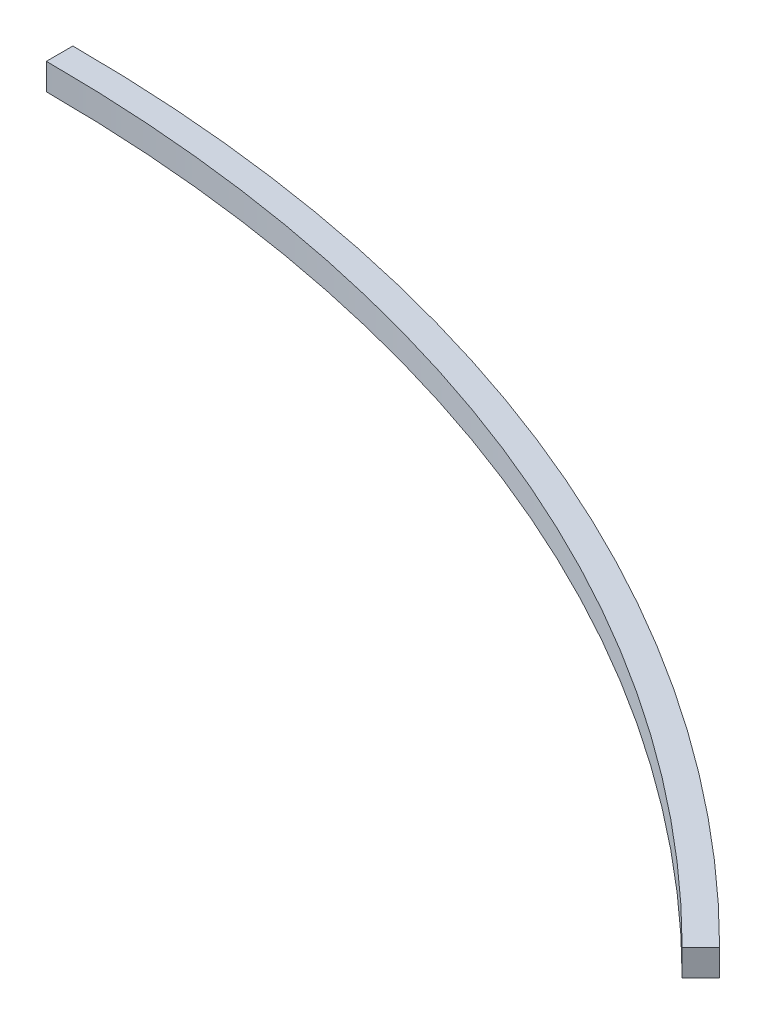
SolidWorks part; units mm, degrees
ref_plane "Front Plane" through (0, 0, 0) normal (0, 0, 1) x (1, 0, 0)
ref_plane "Top Plane" through (0, 0, 0) normal (0, 1, 0) x (1, 0, 0)
ref_plane "Right Plane" through (0, 0, 0) normal (1, 0, 0) x (0, 0, -1)
sketch "Sketch1" plane through (0, 0, 0) normal (0, 1, 0) x (1, 0, 0)
  line L0 (0, 0) -> (0, 580) construction
  line L1 (0, 580) -> (0, 590)
  line L2 (0, 0) -> (417.193, 417.193) construction
  line L3 (410.1219, 410.1219) -> (417.193, 417.193)
  arc A0 (0, 580) -> (410.1219, 410.1219) centre (0, 0) cw
  arc A1 (0, 590) -> (417.193, 417.193) centre (0, 0) cw
  dimension "D1" = 580
  dimension "D2" = 10
  dimension "D3" = 45
  dimension "D4" = 590
extrude "Boss-Extrude1" add sketch "Sketch1" along normal blind 10 contours A1 L1 A0 L3
